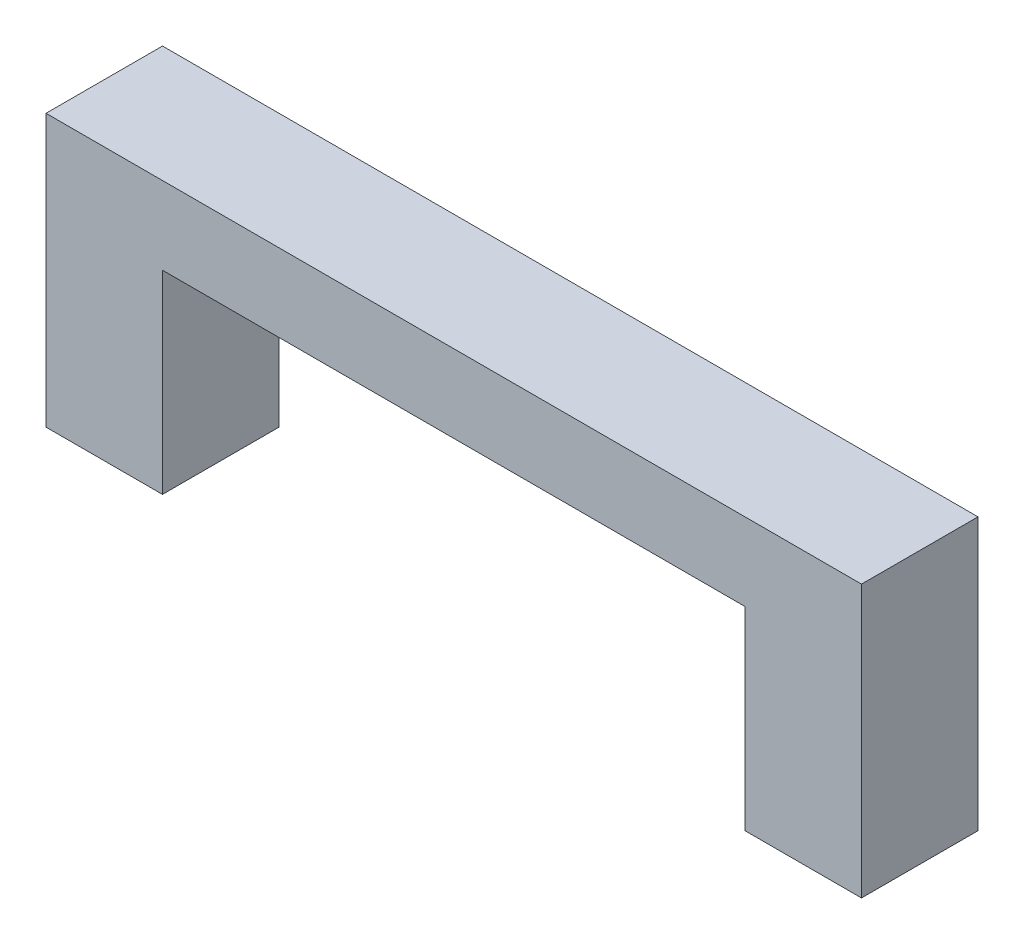
SolidWorks part; units mm, degrees
ref_plane "Front Plane" through (0, 0, 0) normal (0, 0, 1) x (1, 0, 0)
ref_plane "Top Plane" through (0, 0, 0) normal (0, 1, 0) x (1, 0, 0)
ref_plane "Right Plane" through (0, 0, 0) normal (1, 0, 0) x (0, 0, -1)
sketch "Sketch1" plane through (0, 0, 0) normal (0, 0, 1) x (1, 0, 0)
  line L0 (0, 0) -> (0, 7)
  line L1 (0, 7) -> (21, 7)
  line L2 (21, 7) -> (21, 0)
  line L3 (21, 0) -> (18, 0)
  line L4 (18, 0) -> (18, 5)
  line L5 (18, 5) -> (3, 5)
  line L6 (3, 5) -> (3, 0)
  line L7 (3, 0) -> (0, 0)
  point P9 (1.5, 0)
  point P10 (19.5, 0)
  dimension "D1" = 3
  dimension "D2" = 5
  dimension "D3" = 7
  dimension "D4" = 18
extrude "Boss-Extrude1" add sketch "Sketch1" along normal blind 3
sketch "Sketch2" plane through (0, 0, 0) normal (0, -1, 0) x (1, 0, 0)
  line L0 (3, 3) -> (3, 0) construction
  line L1 (0.5, 2.5) -> (2.5, 2.5)
  line L2 (0.5, 2.5) -> (0.5, 0.5)
  line L3 (0.5, 0.5) -> (2.5, 0.5)
  line L4 (2.5, 2.5) -> (2.5, 0.5)
  line L5 (0.5, 2.5) -> (2.5, 0.5) construction
  line L6 (0.5, 0.5) -> (2.5, 2.5) construction
  line L7 (18.5, 2.5) -> (20.5, 2.5)
  line L8 (18.5, 2.5) -> (18.5, 0.5)
  line L9 (18.5, 0.5) -> (20.5, 0.5)
  line L10 (20.5, 2.5) -> (20.5, 0.5)
  line L11 (18.5, 2.5) -> (20.5, 0.5) construction
  line L12 (18.5, 0.5) -> (20.5, 2.5) construction
  line L13 (0, 3) -> (3, 3) construction
  line L14 (21, 3) -> (21, 0) construction
  line L15 (18, 3) -> (21, 3) construction
  point P4 (1.5, 1.5)
  point P9 (19.5, 1.5)
  point P12 (3, 1.5)
  point P15 (1.5, 3)
  point P19 (21, 1.5)
  point P23 (19.5, 3)
  dimension "D1" = 2
extrude "Cut-Extrude1" cut sketch "Sketch2" against normal blind 2.2 contours L10 L7 L8 L9 | L1 L4 L3 L2
